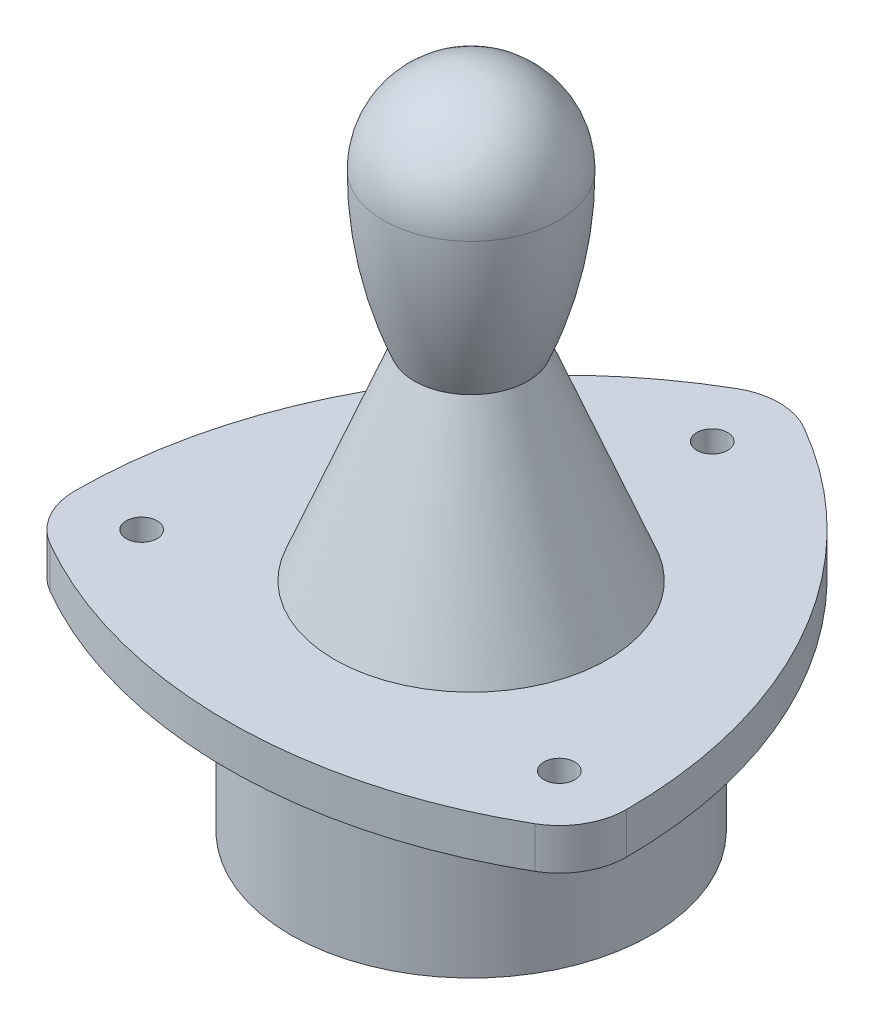
SolidWorks part; units mm, degrees
ref_plane "Спереди" through (0, 0, 0) normal (0, 0, 1) x (1, 0, 0)
ref_plane "Сверху" through (0, 0, 0) normal (0, 1, 0) x (1, 0, 0)
ref_plane "Справа" through (0, 0, 0) normal (1, 0, 0) x (0, 0, -1)
sketch "Эскиз1" plane through (0, 0, 0) normal (0, 1, 0) x (1, 0, 0)
  circle A0 centre (0, 0) radius 35
  dimension "D1" = 70
extrude "Бобышка-Вытянуть1" add sketch "Эскиз1" along normal blind 42
sketch "Эскиз2" plane through (0, 42, 0) normal (0, 1, 0) x (1, 0, 0)
  line L0 (0, 46.7654) -> (-40.5, -23.3827) construction
  line L1 (-40.5, -23.3827) -> (40.5, -23.3827) construction
  line L2 (40.5, -23.3827) -> (0, 46.7654) construction
  line L3 (0, 0) -> (0, 46.7654) construction
  line L4 (0, 0) -> (40.5, -23.3827) construction
  line L5 (0, 0) -> (-40.5, -23.3827) construction
  circle A0 centre (0, 0) radius 46.7654 construction
  circle A1 centre (0, 46.7654) radius 3
  circle A2 centre (-40.5, -23.3827) radius 3
  circle A3 centre (40.5, -23.3827) radius 3
  arc A4 (-47, -34.641) -> (47, -34.641) centre (0, 46.7654) ccw
  arc A5 (-6.5, 58.0237) -> (-53.5, -23.3827) centre (40.5, -23.3827) ccw
  arc A6 (53.5, -23.3827) -> (6.5, 58.0237) centre (-40.5, -23.3827) ccw
  arc A7 (-6.5, 58.0237) -> (6.5, 58.0237) centre (0, 46.7654) cw
  arc A8 (-53.5, -23.3827) -> (-47, -34.641) centre (-40.5, -23.3827) ccw
  arc A9 (53.5, -23.3827) -> (47, -34.641) centre (40.5, -23.3827) cw
  point P3 (121.9064, -70.3827)
  point P5 (0, 59.7654)
  point P17 (51.7583, -29.8827)
  point P18 (-29.2417, -16.8827)
  point P19 (0, 0)
  point P20 (0, -47.2346)
  point P24 (40.9064, 23.6173)
  dimension "D1" = 75
  dimension "D2" = 6
  dimension "D3" = 91
  dimension "D4" = 10
extrude "Бобышка-Вытянуть2" add sketch "Эскиз2" against normal blind 8
sketch "Эскиз3" plane through (0, 0, 0) normal (1, 0, 0) x (0, 0, -1)
  line L0 (0, 0) -> (0, 128) construction
  line L1 (58.0237, 42) -> (-23.3827, 42) construction
  line L2 (0, 111) -> (17, 111) construction
  line L3 (11, 81) -> (26.5, 42)
  line L4 (26.5, 42) -> (0, 42)
  line L5 (0, 128) -> (0, 42)
  arc A0 (0, 128) -> (17, 111) centre (0, 111) cw
  arc A1 (11, 81) -> (17, 111) centre (-61, 111) ccw
  point P11 (0, 0)
  dimension "D3" = 17
  dimension "D1" = 86
  dimension "D2" = 47
  dimension "D4" = 22
  dimension "D5" = 53
revolve "Повернуть1" add sketch "Эскиз3" angle 360 about L5
